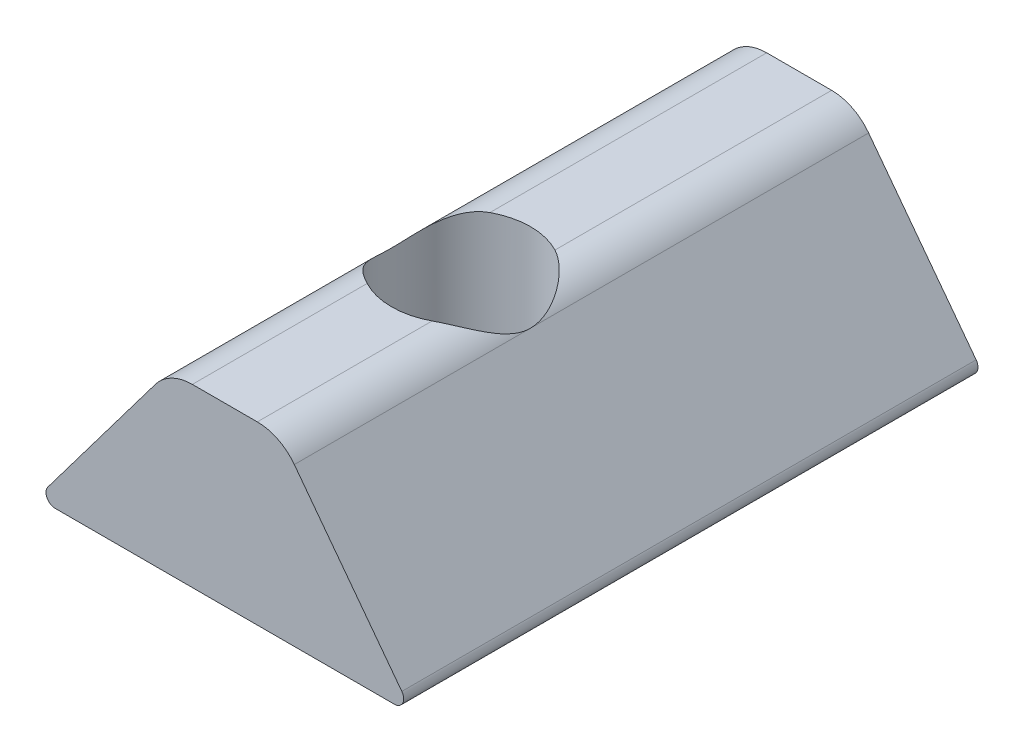
SolidWorks part; units mm, degrees
ref_plane "Front Plane" through (0, 0, 0) normal (0, 0, 1) x (1, 0, 0)
ref_plane "Top Plane" through (0, 0, 0) normal (0, 1, 0) x (1, 0, 0)
ref_plane "Right Plane" through (0, 0, 0) normal (1, 0, 0) x (0, 0, -1)
sketch "Sketch1" plane through (0, 0, 0) normal (0, 0, 1) x (1, 0, 0)
  line L0 (-4.65, 0) -> (4.65, 0)
  line L1 (4.8529, 0.4068) -> (1.9051, 4.3201)
  line L2 (0.8907, 4.826) -> (-0.8907, 4.826)
  line L3 (-1.9051, 4.3201) -> (-4.8529, 0.4068)
  arc A0 (4.65, 0) -> (4.8529, 0.4068) centre (4.65, 0.254) ccw
  arc A1 (-4.65, 0) -> (-4.8529, 0.4068) centre (-4.65, 0.254) cw
  arc A2 (1.9051, 4.3201) -> (0.8907, 4.826) centre (0.8907, 3.556) ccw
  arc A3 (-0.8907, 4.826) -> (-1.9051, 4.3201) centre (-0.8907, 3.556) ccw
  point P3 (0, 4.826)
  point P6 (0, 0)
  point P9 (5.1594, 0)
  point P12 (-5.1594, 0)
  point P15 (1.524, 4.826)
  point P18 (-1.524, 4.826)
  dimension "D4" = 0.254
  dimension "D5" = 1.27
  dimension "D1" = 10.3187
  dimension "D2" = 4.826
  dimension "D3" = 3.048
extrude "Boss-Extrude1" add sketch "Sketch1" against normal blind 15.748
sketch "Sketch2" plane through (0, 0, 0) normal (0, -1, 0) x (1, 0, 0)
  circle A0 centre (0, -6.477) radius 1.905
  point P2 (0, -4.572)
  dimension "D1" = 3.81
  dimension "D2" = 4.572
extrude "Cut-Extrude1" cut sketch "Sketch2" against normal blind 7.62
